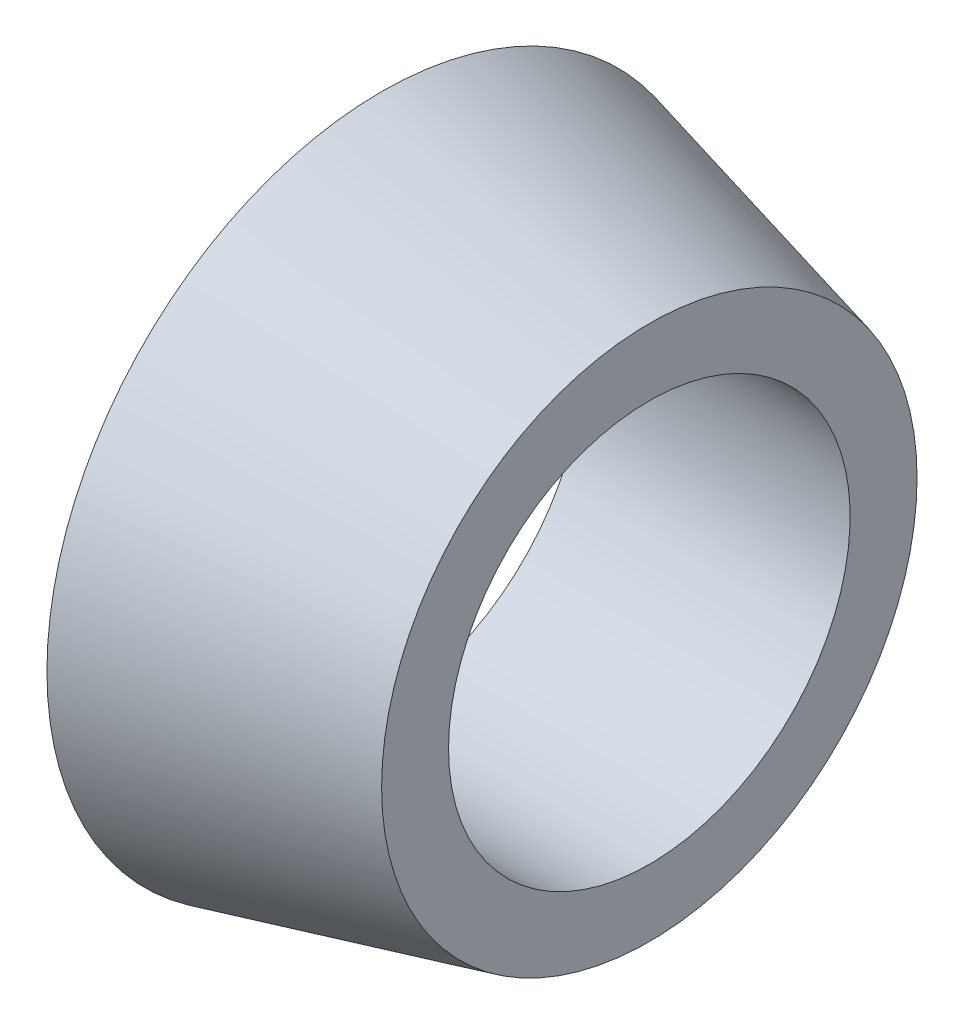
SolidWorks part; units mm, degrees
ref_plane "Płaszczyzna XY" through (0, 0, 0) normal (0, 0, 1) x (1, 0, 0)
ref_plane "Płaszczyzna XZ" through (0, 0, 0) normal (0, 1, 0) x (1, 0, 0)
ref_plane "Płaszczyzna YZ" through (0, 0, 0) normal (1, 0, 0) x (0, 0, -1)
sketch "Szkic1" plane through (0, 0, 0) normal (0, 0, 1) x (1, 0, 0)
  line L0 (0, 6) -> (0, 10)
  line L1 (0, 10) -> (8, 8)
  line L2 (8, 8) -> (8, 6)
  line L3 (8, 6) -> (0, 6)
  line L4 (0, 0) -> (22.8523, 0) construction
  dimension "D1" = 12
  dimension "D2" = 8
  dimension "D3" = 8
  dimension "D4" = 10
revolve "Obrót1" add sketch "Szkic1" angle 360 about L4
